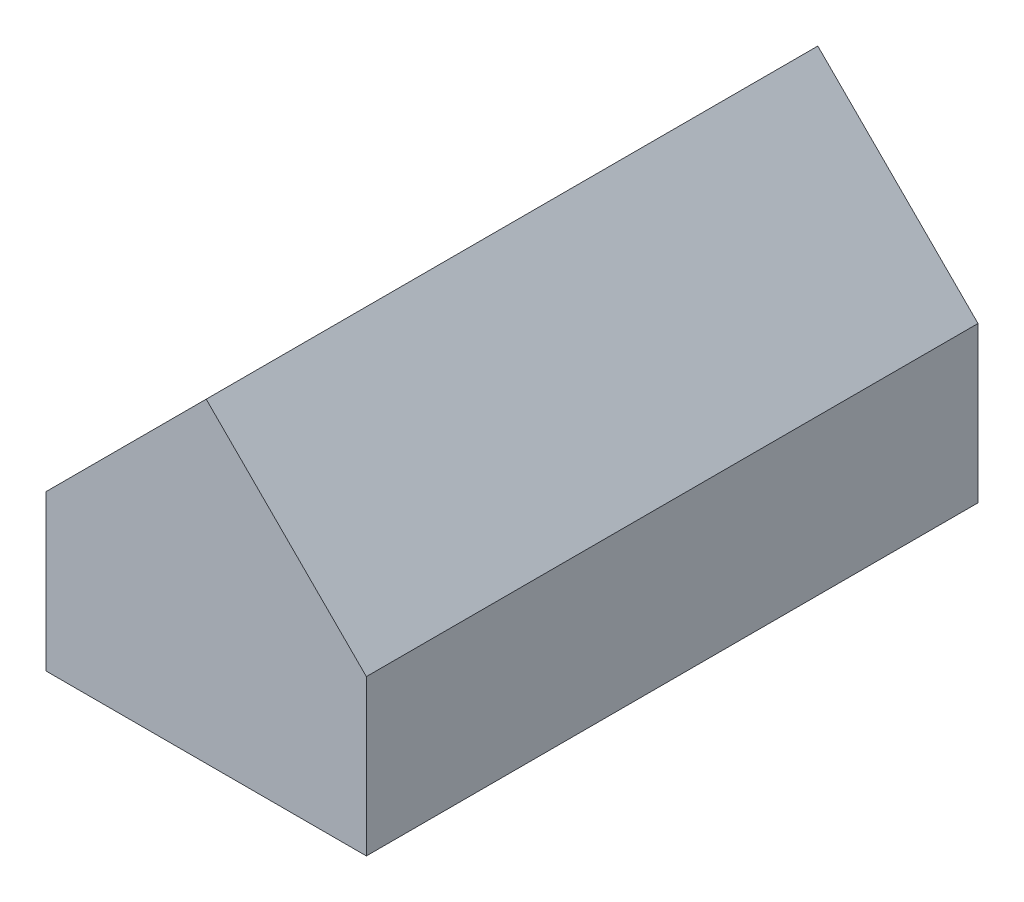
SolidWorks part; units mm, degrees
ref_plane "前视基准面" through (0, 0, 0) normal (0, 0, 1) x (1, 0, 0)
ref_plane "上视基准面" through (0, 0, 0) normal (0, 1, 0) x (1, 0, 0)
ref_plane "右视基准面" through (0, 0, 0) normal (1, 0, 0) x (0, 0, -1)
sketch "草图1" plane through (0, 0, 0) normal (0, 0, 1) x (1, 0, 0)
  line L0 (0, 0) -> (-150, 0)
  line L2 (0, 0) -> (0, 1600)
  line L4 (3000, -0.0003) -> (3000, 1599.9997)
  line L5 (1500.0001, 3099.9999) -> (0, 1600)
  line L6 (1500.0001, 3099.9999) -> (3000, 1599.9997)
  line L7 (-150, 0) -> (-150, 1600)
  line L8 (-150, 1600) -> (1500.0001, 3249.9999)
  line L9 (1500.0001, 3249.9999) -> (3150, 1599.9997)
  line L10 (3150, 1599.9997) -> (3150, -0.0003)
  line L11 (3150, -0.0003) -> (3000, -0.0003)
  dimension "D1" = 3000
  dimension "D2" = 1600
  dimension "D3" = 2121.3203
  dimension "D4" = 2121.3203
  dimension "D5" = 90
  dimension "D6" = 150
  dimension "D7" = 150
  dimension "D8" = 1600
  dimension "D9" = 1600
  dimension "D10" = 2333.4524
extrude "凸台-拉伸1" add sketch "草图1" along normal blind 6100
sketch "草图4" plane through (0, 0, 0) normal (0, 0, -1) x (-1, 0, 0)
  line L0 (-3150, 1599.9997) -> (-3150, -0.0003)
  line L1 (-3150, -0.0003) -> (150, 0)
  line L2 (150, 0) -> (150, 1600)
  line L3 (150, 1600) -> (-1500.0001, 3249.9999)
  line L4 (-1500.0001, 3249.9999) -> (-3150, 1599.9997)
extrude "凸台-拉伸4" add sketch "草图4" along normal blind 100
sketch "草图5" plane through (0, 0, 6100) normal (0, 0, 1) x (1, 0, 0)
  line L0 (-150, 1600) -> (-150, 0)
  line L1 (-150, 0) -> (3150, -0.0003)
  line L2 (3150, -0.0003) -> (3150, 1599.9997)
  line L3 (3150, 1599.9997) -> (1500.0001, 3249.9999)
  line L4 (1500.0001, 3249.9999) -> (-150, 1600)
extrude "凸台-拉伸5" add sketch "草图5" along normal blind 100
sketch "草图3" plane through (0, 0, 0) normal (0, 0, -1) x (-1, 0, 0)
  line L0 (-3150, 0) -> (-3150, 1599.9997)
  line L1 (-3150, 1599.9997) -> (-1500.0001, 3249.9999)
  line L2 (-1500.0001, 3249.9999) -> (150, 1600)
  line L3 (150, 1600) -> (150, 0)
  line L4 (150, 0) -> (-3150, 0)
extrude "凸台-拉伸3" add sketch "草图3" along normal blind 50
